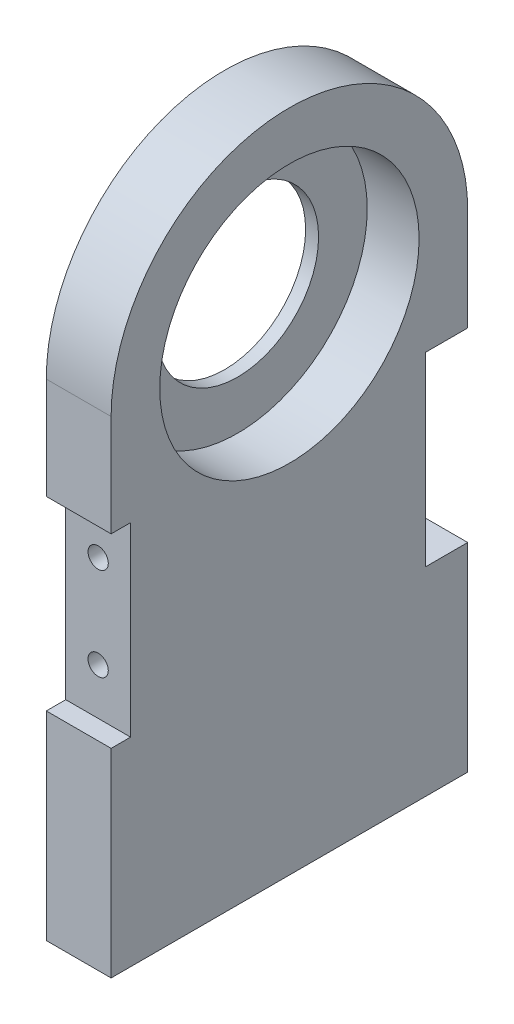
SolidWorks part; units mm, degrees
ref_plane "Front Plane" through (0, 0, 0) normal (0, 0, 1) x (1, 0, 0)
ref_plane "Top Plane" through (0, 0, 0) normal (0, 1, 0) x (1, 0, 0)
ref_plane "Right Plane" through (0, 0, 0) normal (1, 0, 0) x (0, 0, -1)
sketch "Sketch2" plane through (0, 0, 0) normal (1, 0, 0) x (0, 0, -1)
  line L1 (55, 75) -> (-55, 75)
  line L2 (55, 75) -> (55, -75)
  line L3 (55, -75) -> (-55, -75)
  line L4 (-55, 75) -> (-55, -75)
  line L5 (55, 75) -> (-55, -75) construction
  line L6 (55, -75) -> (-55, 75) construction
  circle A0 centre (0, 75) radius 55
  point P0 (0, 0)
  dimension "D1" = 110
  dimension "D2" = 150
extrude "Boss-Extrude1" add sketch "Sketch2" along normal blind 20 contours A0 L4 L3 L2 | L1 A0 | L1 A0
sketch "Sketch3" plane through (20, 0, 0) normal (1, 0, 0) x (0, 0, -1)
  circle A0 centre (0, 75) radius 40
extrude "Cut-Extrude1" cut sketch "Sketch3" against normal blind 16
sketch "Sketch4" plane through (4, 0, 0) normal (1, 0, 0) x (0, 0, -1)
  circle A0 centre (0, 75) radius 25
extrude "Cut-Extrude2" cut sketch "Sketch4" against normal blind 11.1125
sketch "Sketch5" plane through (0, -75, 0) normal (0, -1, 0) x (1, 0, 0)
  line L0 (10, 55) -> (10, -55) construction
  line L1 (20, 55) -> (0, 55) construction
  line L2 (20, -55) -> (0, -55) construction
  point P6 (10, 36.6667)
  point P7 (10, 18.3333)
  point P8 (10, 0)
  point P9 (10, -18.3333)
  point P10 (10, -36.6667)
hole_wizard "Tap Drill for M6x1.0 Tap2" positions "Sketch9" profile "Sketch10" hole size "M6x1.0" standard "ANSI Metric"
sketch "Sketch9" plane through (0, -75, 0) normal (0, -1, 0) x (-1, 0, 0)
  line L0 (-10, -55) -> (-10, 55) construction
  point P0 (-10, -36.6667)
  point P3 (-10, -18.3333)
  point P6 (-10, 0)
  point P10 (-10, 18.3333)
  point P13 (-10, 36.6667)
sketch "Sketch10" plane through (10, -75, 36.6667) normal (1, 0, 0) x (0, 0, -1)
  line L0 (0, 0) -> (0, 41.5022)
  line L1 (0, 41.5022) -> (2.5, 40)
  line L2 (2.5, 40) -> (2.5, 0)
  line L5 (2.5, 0) -> (0, 0)
  line L10 (0, 41.5022) -> (-2.5, 40) construction
  line L11 (0, -6.35) -> (0, 107.95) construction
  dimension "Hole Dia." = 5
  dimension "Hole Depth" = 40
  dimension "Drill Angle" = 118
sketch "Sketch11" plane through (0, 0, 0) normal (-1, 0, 0) x (0, 0, 1)
  line L0 (0, 35) -> (0, 15) construction
  line L1 (0, 75) -> (0, 35) construction
  line L2 (-55, 15) -> (55, 15) construction
  line L3 (55, 75) -> (55, -75) construction
  circle A0 centre (0, 75) radius 40 construction
  point P11 (0, 15)
  dimension "D1" = 80
  dimension "D2" = 20
sketch "Sketch12" plane through (20, 0, 0) normal (1, 0, 0) x (0, 0, -1)
  line L0 (-55, 43.65) -> (-55, -13.65)
  line L1 (55, 43.65) -> (42, 43.65)
  line L2 (-55, 75) -> (-55, -75) construction
  line L3 (-55, 43.65) -> (-49, 43.65)
  line L4 (-49, 43.65) -> (-49, -13.65)
  line L5 (-49, -13.65) -> (-55, -13.65)
  line L6 (55, 43.65) -> (55, -13.65)
  line L7 (42, 43.65) -> (42, -13.65)
  line L8 (55, 75) -> (55, -75) construction
  line L9 (42, -13.65) -> (55, -13.65)
  point P4 (-55, 15)
  point P13 (55, 15)
  dimension "D1" = 57.3
  dimension "D2" = 57.3
extrude "Cut-Extrude3" cut sketch "Sketch12" against normal blind 20
sketch "Sketch13" plane through (0, 0, 49) normal (0, 0, 1) x (1, 0, 0)
  line L0 (10, 43.65) -> (10, -13.65) construction
  line L1 (0, 43.65) -> (20, 43.65) construction
  line L2 (0, -13.65) -> (20, -13.65) construction
  point P6 (10, 29.325)
  point P7 (10, 15)
  point P8 (10, 0.675)
hole_wizard "Tap Drill for M6 Helicoil1" positions "3DSketch1" profile "Sketch14" hole size "M6x1.0" standard "ANSI Metric"
sketch3d "3DSketch1"
  point P0 (10, 29.325, 49)
  point P3 (10, 0.675, 49)
sketch "Sketch14" plane through (10, 29.325, 49) normal (1, 0, 0) x (0, -1, 0)
  line L0 (0, 0) -> (0, 21.8777)
  line L1 (0, 21.8777) -> (3.125, 20)
  line L2 (3.125, 20) -> (3.125, 0)
  line L5 (3.125, 0) -> (0, 0)
  line L10 (0, 21.8777) -> (-3.125, 20) construction
  line L11 (0, -6.35) -> (0, 107.95) construction
  dimension "Hole Dia." = 6.25
  dimension "Hole Depth" = 20
  dimension "Drill Angle" = 118
sketch "Sketch15" plane through (0, 0, -42) normal (0, 0, -1) x (-1, 0, 0)
  line L0 (-10, 43.65) -> (-10, -13.65) construction
  line L1 (0, 43.65) -> (-20, 43.65) construction
  line L2 (0, -13.65) -> (-20, -13.65) construction
  point P6 (-10, 29.325)
  point P7 (-10, 15)
  point P8 (-10, 0.675)
hole_wizard "Tap Drill for M6 Helicoil2" positions "Sketch16" profile "Sketch17" hole size "M6x1.0" standard "ANSI Metric"
sketch "Sketch16" plane through (0, 0, -42) normal (0, 0, -1) x (-1, 0, 0)
  point P0 (-10, 29.325)
  point P3 (-10, 0.675)
sketch "Sketch17" plane through (10, 29.325, -42) normal (1, 0, 0) x (0, 1, 0)
  line L0 (0, 0) -> (0, 21.8777)
  line L1 (0, 21.8777) -> (3.125, 20)
  line L2 (3.125, 20) -> (3.125, 0)
  line L5 (3.125, 0) -> (0, 0)
  line L10 (0, 21.8777) -> (-3.125, 20) construction
  line L11 (0, -6.35) -> (0, 107.95) construction
  dimension "Hole Dia." = 6.25
  dimension "Hole Depth" = 20
  dimension "Drill Angle" = 118
equation "\"GearDiameter\"= 80mm"
equation "\"WormGearDiam\"= 40mm"
equation "\"WormLength\"= 40mm"
equation "\"WormHubDiam\"= 25mm"
equation "\"D1@Sketch11\"=\"GearDiameter\""
equation "\"D2@Sketch11\"=\"WormGearDiam\" /2"
